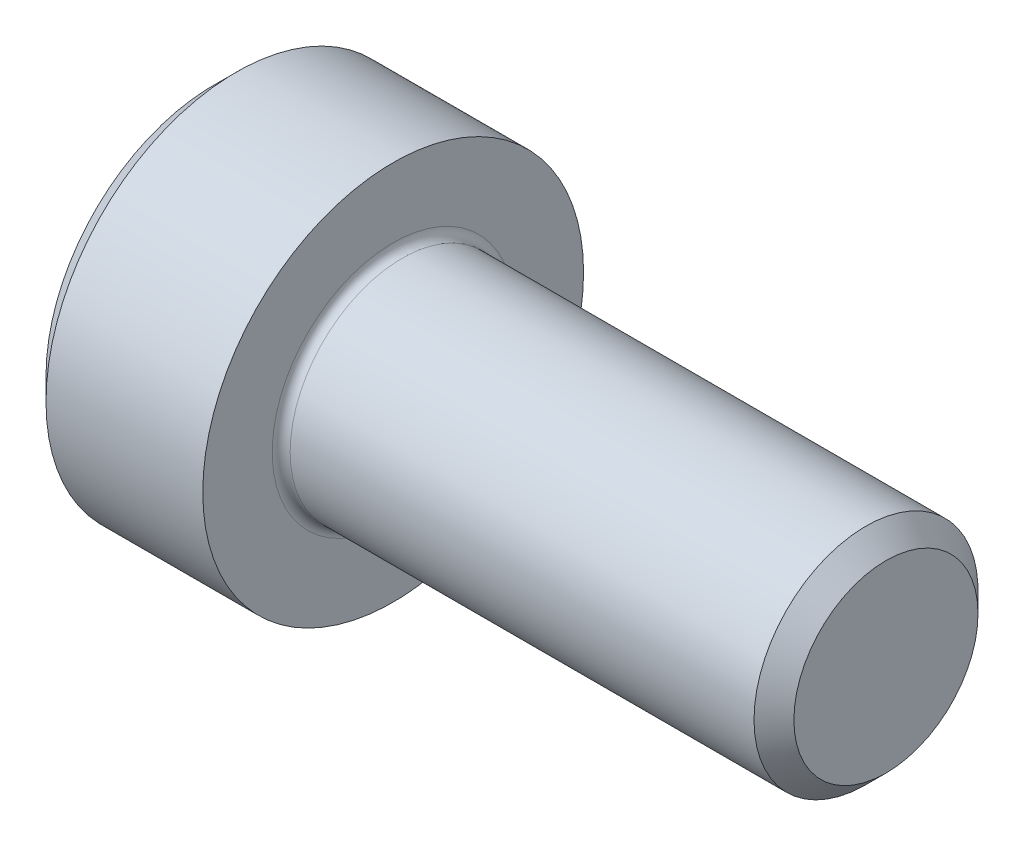
SolidWorks part; units mm, degrees
revolve "Base-Revolve" add sketch "BodySke"
sketch "BodySke" plane through (0, 0, 0) normal (0, 0, 1) x (1, 0, 0)
  line L0 (0, 0) -> (0, 3.75)
  line L1 (0.5, 4.25) -> (4, 4.25)
  line L2 (4, 4.25) -> (4, 2.5)
  line L3 (4, 2.5) -> (14.555, 2.5)
  line L4 (15, 2.055) -> (15, 0)
  line L5 (15, 0) -> (0, 0)
  line L6 (-31.75, 0) -> (127, 0) construction
  line L7 (0, 3.75) -> (0.5, 4.25)
  line L8 (15, 2.055) -> (14.555, 2.5)
  line L9 (0, -3.75) -> (0.5, -4.25) construction
  line L10 (15, -2.055) -> (14.555, -2.5) construction
  line L11 (4.8, 9.525) -> (4.8, 3.175) construction
  line L12 (5, 9.525) -> (5, 3.175) construction
  line L13 (-35, 9.525) -> (-35, 3.175) construction
  dimension "Diameter" = 5
  dimension "Head_ht" = 4
  dimension "Length" = 11
  dimension "Body_ch_ang" = 45
  dimension "Head_dia" = 8.5
  dimension "Head_ch_ang" = 45
  dimension "Minor_dia" = 4.11
  dimension "Advance" = 0.8
  dimension "Thread_nom" = 10
  dimension "Thread_length" = 50
  dimension "Head_ch_ht" = 0.5
cosmetic thread "ThreadCosmetic"
fillet "Fillet1" radius 0.2 1 edges at (4, 0, 2.5)
ref_plane "Plane1" through (0, 0, 0) normal (0, 0, 1) x (1, 0, 0)
ref_plane "Plane2" through (0, 0, 0) normal (0, 1, 0) x (1, 0, 0)
ref_plane "Plane3" through (0, 0, 0) normal (1, 0, 0) x (0, 0, -1)
sketch "Sketch2" plane through (0, 0, 0) normal (0, 0, 1) x (1, 0, 0)
  line L0 (0, 2.042) -> (2.5, 2.042)
  line L1 (2.5, 2.042) -> (3.6789, 0)
  line L2 (-31.75, 0) -> (127, 0) construction
  line L3 (3.6789, 0) -> (0, 0)
  line L4 (0, 0) -> (0, 2.042)
  line L5 (0, 3.75) -> (0, -3.75) construction
  line L6 (0, 0) -> (47.625, 0) construction
  line L7 (4, -4.25) -> (4, 4.25) construction
  dimension "D1" = 2.042
  dimension "D2" = 60
revolve "Hex-PreBroach" cut sketch "Sketch2" angle 360 about L6
sketch "Sketch3" plane through (0, 0, 0) normal (-1, 0, 0) x (0, 0.5, 0.866)
  line L0 (1.1789, 2.042) -> (-1.1789, 2.042)
  line L1 (-1.1789, 2.042) -> (-2.3579, 0)
  line L2 (1.1789, 2.042) -> (2.3579, 0)
  line L3 (1.1789, -2.042) -> (2.3579, 0)
  line L4 (1.1789, -2.042) -> (-1.1789, -2.042)
  line L5 (-1.1789, -2.042) -> (-2.3579, 0)
  dimension "D1" = 2.042
  dimension "D2" = 2.042
  dimension "Hex_size" = 4.084
extrude "Hex" cut sketch "Sketch3" against normal blind 2.5
sketch "Sketch4" plane through (0, 0, 0) normal (-1, 0, 0) x (0, 0, 1)
  line L0 (0, 0) -> (2.3876, 0)
  line L1 (0, 0) -> (6.1484, 3.5498) construction
  line L2 (0, 0) -> (1.1938, 2.0677)
  line L3 (1.9883, 0.576) -> (2.2704, 0.7389)
  line L4 (1.493, 1.4339) -> (1.7751, 1.5968)
  arc A0 (1.9883, 0.576) -> (1.493, 1.4339) centre (0, 0) ccw
  arc A1 (2.3876, 0) -> (2.2704, 0.7389) centre (0, 0) ccw
  arc A2 (1.1938, 2.0677) -> (1.7751, 1.5968) centre (0, 0) cw
  dimension "D1" = 30
  dimension "D2" = 60
  dimension "Spline_p_dim" = 0.9906
  dimension "D3" = 0.4953
extrude "Spline" [suppressed] cut sketch "Sketch4" against normal blind 2.5
pattern_circular "CirPattern1" [suppressed] count 6 every 60
sketch "Sketch5" plane through (0, 0, 0) normal (0, 0, 1) x (1, 0, 0)
  line L0 (-31.75, 0) -> (127, 0) construction
  line L2 (0, 3.75) -> (0, -3.75) construction
  circle A0 centre (2, 0) radius 0.675
  dimension "Drilled_hole_dia" = 1.35
  dimension "Drilled_hole_loc" = 2
extrude "Hole" [suppressed] cut sketch "Sketch5" against normal through all and the other way through all
pattern_circular "Drilled-4" [suppressed] count 2 every 60
pattern_circular "Drilled-6" [suppressed] count 3 every 60
sketch "ThdSchSke" plane through (0, 0, 0) normal (0, 0, 1) x (1, 0, 0)
  line L0 (5, -2.055) -> (4.6884, -2.5)
  line L1 (5, -2.055) -> (5.3116, -2.5)
  line L2 (5.3116, -2.5) -> (5.3116, -3.125)
  line L3 (-3.175, 0) -> (5.1513, 0) construction
  line L5 (5.3116, -3.125) -> (4.6884, -3.125)
  line L6 (4.6884, -3.125) -> (4.6884, -2.5)
  line L7 (0, 3.75) -> (0, -3.75) construction
  dimension "Thread_minor" = 4.11
  dimension "Diameter" = 5
  dimension "Start" = 5
revolve "ThreadSchematic" [suppressed] cut sketch "ThdSchSke" angle 360 about L3
pattern_linear "ThdSchPat" [suppressed]
equation "\"D2@Sketch3\" = \"Hex_size@Sketch3\" / 2"
equation "\"D1@Sketch3\" = \"Hex_size@Sketch3\" / 2"
equation "\"D1@Sketch2\" = \"Hex_size@Sketch3\" / 2"
equation "\"D3@Sketch4\" = \"Spline_p_dim@Sketch4\" / 2"
equation "\"Thread_minor@ThreadCosmetic\"  =  \"Minor_dia@BodySke\""
equation "\"D2@CirPattern1\" = 360 / \"Num_teeth@CirPattern1\""
equation "\"Wall_thickness@Sketch2\" = \"Head_ht@BodySke\" - \"Key_eng@Hex\""
equation "\"Thread_length@ThreadCosmetic\" = ((sgn( (\"Length@BodySke\" - \"Advance@BodySke\" ) - \"Thread_nom@BodySke\" )-1)*( (\"Length@BodySke\" - \"Advance@BodySke\" ) - \"Thread_nom@BodySke\" ))/-2+ \"Thread_nom@BodySke\""
equation "\"Thread_minor@ThdSchSke\" = \"Minor_dia@BodySke\""
equation "\"Diameter@ThdSchSke\" = \"Diameter@BodySke\""
equation "\"Overcut@ThdSchSke\" = \"Diameter@BodySke\" * 1.25"
equation "\"Start@ThdSchSke\" = \"Head_ht@BodySke\" + \"Length@BodySke\" - \"Thread_length@ThreadCosmetic\"  '---Non-countersunk---"
equation "\"Num_threads@ThdSchPat\" = int( \"Thread_length@ThreadCosmetic\" / \"Advance@BodySke\" + 0.999 )  + 1"
equation "\"Advance@ThdSchPat\" = \"Thread_length@ThreadCosmetic\" /  (\"Num_threads@ThdSchPat\" - 1) 'relax it"
equation "\"Num_threads@ThdSchPat\" = \"Num_threads@ThdSchPat\" - sgn( \"Num_threads@ThdSchPat\" - 1) '---chamfered tips only---"
